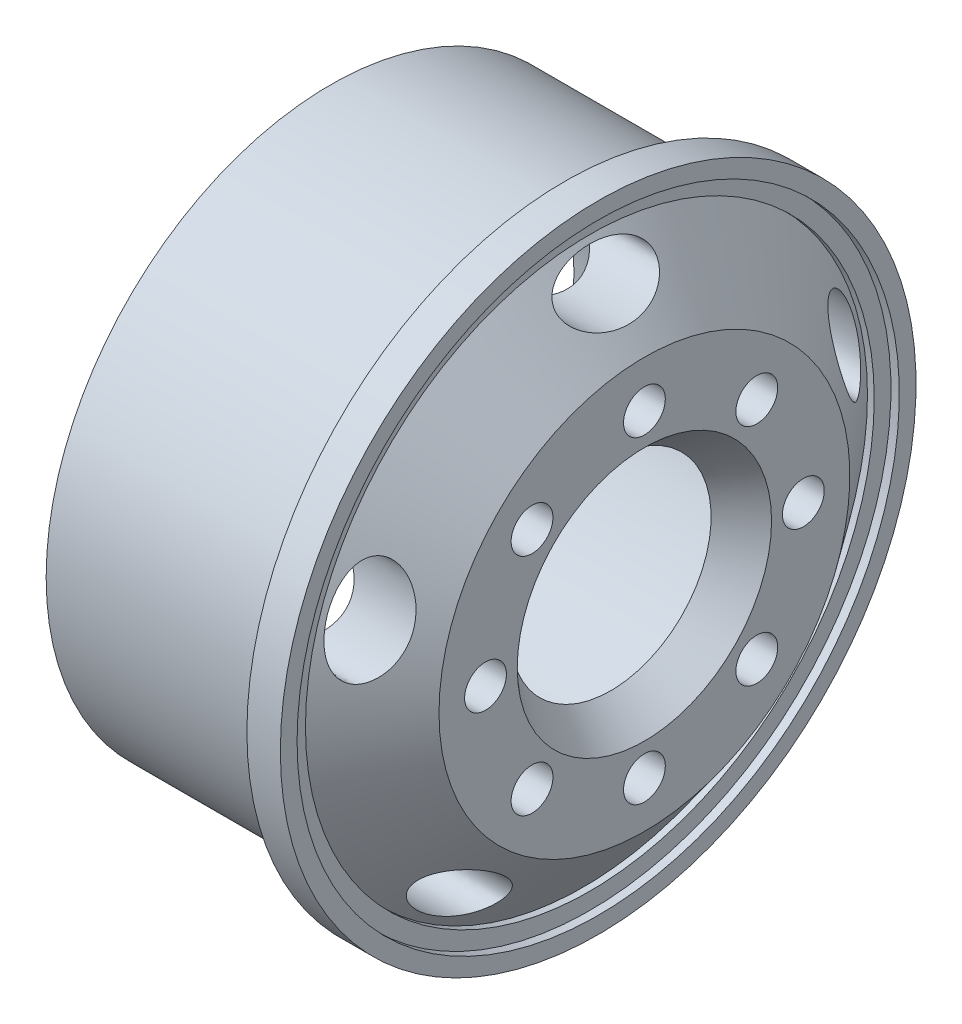
SolidWorks part; units mm, degrees
ref_plane "Front Plane" through (0, 0, 0) normal (0, 0, 1) x (1, 0, 0)
ref_plane "Top Plane" through (0, 0, 0) normal (0, 1, 0) x (1, 0, 0)
ref_plane "Right Plane" through (0, 0, 0) normal (1, 0, 0) x (0, 0, -1)
sketch "Sketch1" plane through (0, 0, 0) normal (0, 1, 0) x (1, 0, 0)
  line L0 (-37.2789, 0) -> (44.8184, 0) construction
  line L27 (2.9431, 14.55) -> (6.9363, 11.5409)
  line L28 (4.1863, 17) -> (4.1863, 19)
  line L29 (4.1863, 19) -> (5.6863, 19)
  line L34 (6.9363, 11.5409) -> (6.9363, 6)
  line L37 (8.9491, 12.2802) -> (8.9491, 7.6018)
  line L38 (6.9363, 6) -> (8.9491, 7.6018)
  line L39 (5.6863, 19) -> (6.1863, 19)
  line L40 (6.1863, 19) -> (6.1863, 18)
  line L41 (6.1863, 18) -> (5.6863, 18)
  line L42 (4.1863, 17) -> (-9.8137, 17)
  line L43 (-9.8137, 17) -> (-9.8137, 14.55)
  line L44 (-9.8137, 14.55) -> (2.9431, 14.55)
  line L45 (5.6863, 18) -> (5.6863, 17)
  line L46 (5.6863, 17) -> (5.2833, 17)
  line L49 (5.2833, 17) -> (8.9491, 12.2802)
  point P3 (8.936, 7.0891)
  point P4 (7.9363, 16.8502)
  point P5 (4.0798, 13.7427)
  point P16 (8.0798, 11.847)
  dimension "D2" = 12
  dimension "D4" = 14
  dimension "D5" = 1
  dimension "D6" = 1.5
  dimension "D7" = 29.1
  dimension "D8" = 3.9932
  dimension "D9" = 2
  dimension "D10" = 1
  dimension "D11" = 0.5
  dimension "D12" = 34
  dimension "D3" = 5
  dimension "D15" = 16.75
  dimension "D16" = 2.45
  dimension "D17" = 38
  dimension "D19" = 23.0818
revolve "Revolve1" add sketch "Sketch1" angle 360 about L0
sketch "Sketch2" plane through (8.9491, 0, 0) normal (1, 0, 0) x (0, 0, -1)
  circle A0 centre (0, 0) radius 9.5 construction
  circle A1 centre (0, 9.5) radius 1.25
  circle A2 centre (6.7175, 6.7175) radius 1.25
  circle A3 centre (9.5, 0) radius 1.25
  circle A4 centre (6.7175, -6.7175) radius 1.25
  circle A5 centre (0, -9.5) radius 1.25
  circle A6 centre (-6.7175, -6.7175) radius 1.25
  circle A7 centre (-9.5, 0) radius 1.25
  circle A8 centre (-6.7175, 6.7175) radius 1.25
  point P22 (0, 0)
  dimension "D1" = 19
  dimension "D2" = 2.5
  dimension "D3" = 8
extrude "Cut-Extrude1" cut sketch "Sketch2" against normal through all
ref_plane "Plane1" through (0, 0, 15) normal (0, 0, 1) x (1, 0, 0)
sketch "Sketch3" plane through (8.9491, 0, 0) normal (1, 0, 0) x (0, 0, -1)
  circle A0 centre (0, 0) radius 15 construction
  ellipse E0 centre (0, 15) end of major axis (3, 15) minor radius 1.5
  ellipse E1 centre (14.2658, 4.6353) end of major axis (15.1929, 1.7821) minor radius 1.5
  ellipse E2 centre (8.8168, -12.1353) end of major axis (6.3897, -13.8986) minor radius 1.5
  ellipse E3 centre (-8.8168, -12.1353) end of major axis (-11.2438, -10.3719) minor radius 1.5
  ellipse E4 centre (-14.2658, 4.6353) end of major axis (-13.3388, 7.4884) minor radius 1.5
  point P36 (0, 0)
  dimension "D1" = 30
  dimension "D2" = 6
  dimension "D3" = 3
  dimension "D4" = 5
extrude "Cut-Extrude2" cut sketch "Sketch3" against normal up to surface (6.9973 mm away)
